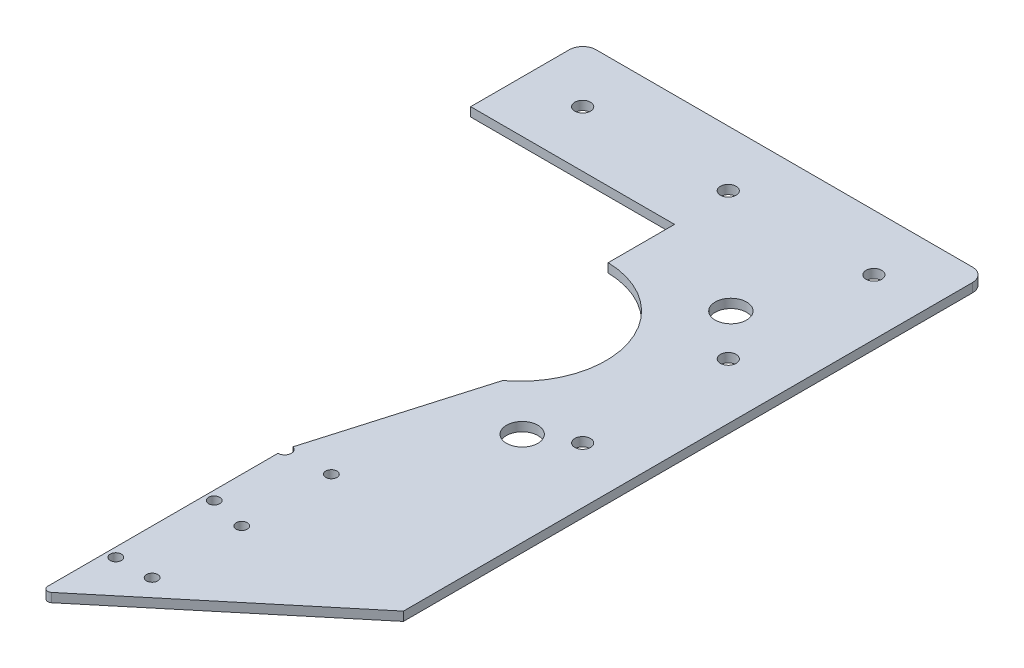
SolidWorks part; units mm, degrees
ref_plane "Спереди" through (0, 0, 0) normal (0, 0, 1) x (1, 0, 0)
ref_plane "Сверху" through (0, 0, 0) normal (0, 1, 0) x (1, 0, 0)
ref_plane "Справа" through (0, 0, 0) normal (1, 0, 0) x (0, 0, -1)
sketch "Эскиз1" plane through (0, 0, 0) normal (0, 1, 0) x (1, 0, 0)
  line L0 (-57.0454, 34.1949) -> (32.9546, 34.1949)
  line L1 (32.9546, 34.1949) -> (32.9546, -95.8051)
  line L2 (-57.0454, 34.1949) -> (-57.0454, 9.1949)
  line L3 (-57.0454, 9.1949) -> (17.4546, 9.1949)
  line L4 (17.4546, 9.1949) -> (17.4546, -55.8051)
  line L5 (17.4546, -55.8051) -> (-11.5454, -55.8051)
  line L6 (-11.5454, -55.8051) -> (-11.5454, -132.8051)
  line L7 (-11.5454, -132.8051) -> (32.9546, -95.8051)
  line L8 (-57.0454, 34.1949) -> (-57.0454, 21.6949) construction
  line L9 (-57.0454, 21.6949) -> (32.9546, 21.6949) construction
  line L10 (-57.0454, 21.6949) -> (-44.5454, 21.6949) construction
  line L11 (32.9546, 21.6949) -> (20.4546, 21.6949) construction
  line L12 (17.4546, 5.3717) -> (20.4546, 5.3717) construction
  line L13 (20.4546, 34.1949) -> (20.4546, -10.8051) construction
  line L14 (20.4546, 34.1949) -> (20.4546, -43.3051) construction
  circle A0 centre (-44.5454, 21.6949) radius 1.75
  circle A1 centre (-12.0454, 21.6949) radius 1.75
  circle A2 centre (20.4546, 21.6949) radius 1.75
  circle A3 centre (20.4546, -10.8051) radius 1.75
  circle A4 centre (20.4546, -43.3051) radius 1.75
  dimension "D8" = 12.5
  dimension "D9" = 3
  dimension "D1" = 90
  dimension "D2" = 130
  dimension "D3" = 25
  dimension "D4" = 65
  dimension "D5" = 77
  dimension "D6" = 74.5
  dimension "D7" = 12.5
  dimension "D10" = 29
  dimension "D12" = 45
  dimension "D13" = 77.5
sketch "Эскиз3" plane through (0, 0, 0) normal (0, 1, 0) x (1, 0, 0)
  line L0 (-56.5429, 9.1949) -> (18.4571, 9.1949)
extrude "Бобышка-Вытянуть1" add sketch "Эскиз1" along normal blind 2
sketch "Эскиз4" plane through (0, 2, 0) normal (0, 1, 0) x (1, 0, 0)
  line L0 (-11.5454, -55.8051) -> (-11.5454, 9.1949)
  line L1 (-56.5429, 9.1949) -> (18.4571, 9.1949) construction
  line L2 (-11.5454, 9.1949) -> (18.4571, 9.1949)
  line L3 (18.4571, 9.1949) -> (17.4546, -55.8051)
  line L4 (17.4546, -55.8051) -> (-11.5454, -55.8051)
  circle A0 centre (12.0271, -48.3751) radius 3.5
  circle A1 centre (11.4932, -1.2665) radius 3.5
  dimension "D1" = 7
extrude "Бобышка-Вытянуть2" add sketch "Эскиз4" against normal up to surface (2 mm away) contours A0 L0 A1 M5 M4 M6 up to face at (-4.5454, 0, 31.6801)
sketch "Эскиз5" plane through (0, 2, 0) normal (0, 1, 0) x (1, 0, 0)
  circle A0 centre (-12.0454, -24.8051) radius 19.2 construction
  circle A1 centre (-12.0454, -24.8051) radius 19.2
extrude "Вырез-Вытянуть1" cut sketch "Эскиз5" against normal through all both and the other way through all
sketch "Эскиз7" plane through (0, 2, 0) normal (0, 1, 0) x (1, 0, 0)
  line L0 (-0.5454, -40.1801) -> (-11.5454, -77.8093)
  line L3 (-1.5429, -24.8054) -> (-11.5446, -77.8051) construction
  line L4 (-11.5454, -43.9986) -> (-11.5454, -132.8051) construction
  line L5 (-11.5454, -77.8093) -> (-11.5454, -43.9986)
  arc A1 (-0.5454, -40.1801) -> (-11.5454, -43.9986) centre (-12.107, -24.6276) cw
  arc A2 (-11.5454, -43.9986) -> (-11.5454, -5.6116) centre (-12.0454, -24.8051) ccw construction
  dimension "D1" = 11
extrude "Вырез-Вытянуть2" cut sketch "Эскиз7" against normal through all both and the other way through all
fillet "Скругление1" radius 3 2 edges at (-57.0454, 1, -34.1949) (32.9546, 1, -34.1949)
sketch "Эскиз9" plane through (0, 2, 0) normal (0, 1, 0) x (1, 0, 0)
  circle A0 centre (-11.5454, -77.8093) radius 1.5
  dimension "D1" = 3
extrude "Вырез-Вытянуть4" cut sketch "Эскиз9" against normal through all both and the other way through all
fillet "Скругление2" radius 1 1 edges at (-11.5454, 1, 132.8051)
sketch "Эскиз13" plane through (0, 2, 0) normal (0, 1, 0) x (1, 0, 0)
  circle A0 centre (-9.5449, -95.5512) radius 1.25
  circle A1 centre (-9.5449, -117.5083) radius 1.25
extrude "Вырез-Вытянуть6" cut sketch "Эскиз13" against normal through all both and the other way through all
sketch "Эскиз15" plane through (0, 2, 0) normal (0, 1, 0) x (1, 0, 0)
  line L0 (-11.5454, -79.3093) -> (-12.4204, -79.3093) construction
  line L1 (-11.5454, -79.3093) -> (-11.5454, -130.6731) construction
  line L2 (-11.9829, -79.3093) -> (-11.9829, -141.7359) construction
  line L3 (-12.4204, -78.4666) -> (-12.4204, -130.1064) construction
  circle A1 centre (-22.4204, -77.3986) radius 1.25 construction
  circle A2 centre (-22.4204, -97.3986) radius 1.25 construction
  circle A3 centre (-22.4204, -117.3986) radius 1.25 construction
  circle A4 centre (-22.4204, -77.3986) radius 1.25 construction
  circle A5 centre (-22.4204, -97.3986) radius 1.25 construction
  circle A6 centre (-22.4204, -117.3986) radius 1.25 construction
  circle A7 centre (-1.5454, -117.3986) radius 1.25
  circle A8 centre (-1.5454, -97.3986) radius 1.25
  circle A9 centre (-1.5454, -77.3986) radius 1.25
extrude "Вырез-Вытянуть7" cut sketch "Эскиз15" against normal through all both and the other way through all
